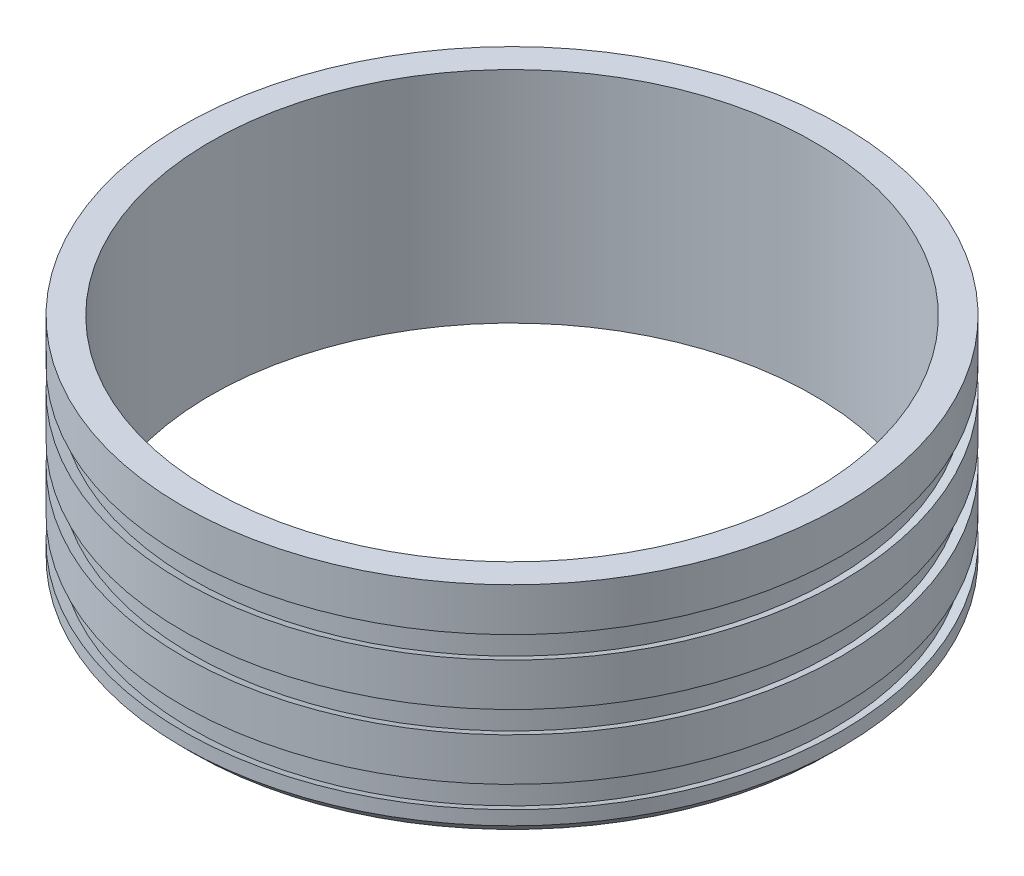
SolidWorks part; units mm, degrees
ref_plane "Front Plane" through (0, 0, 0) normal (0, 0, 1) x (1, 0, 0)
ref_plane "Top Plane" through (0, 0, 0) normal (0, 1, 0) x (1, 0, 0)
ref_plane "Right Plane" through (0, 0, 0) normal (1, 0, 0) x (0, 0, -1)
sketch "Sketch1" plane through (0, 0, 0) normal (0, 1, 0) x (1, 0, 0)
  circle A0 centre (0, 0) radius 76.25
  circle A1 centre (0, 0) radius 69.75
  dimension "D2" = 152.5
  dimension "D1" = 6.5
extrude "Boss-Extrude1" add sketch "Sketch1" along normal blind 50.8
sketch "Sketch2" plane through (0, 0, 0) normal (0, 0, 1) x (1, 0, 0)
  line L0 (-76.25, 40.8) -> (-76.25, 35.72) construction
  line L1 (-76.25, 40.8) -> (-76.25, 35.72)
  line L2 (-76.25, 50.8) -> (-76.25, 0) construction
  line L19 (0, 0) -> (0, 50.8) construction
  line L20 (-76.25, 0) -> (76.25, 0) construction
  line L21 (69.75, 50.8) -> (-69.75, 50.8) construction
  line L22 (-76.25, 40.8) -> (-74, 41.6189)
  line L23 (-74, 41.6189) -> (-74, 34.9011)
  line L24 (-74, 38.26) -> (-76.25, 38.26) construction
  line L25 (-76.25, 35.72) -> (-74, 34.9011)
  line L26 (-74, 26.6189) -> (-74, 19.9011)
  line L27 (-76.25, 20.72) -> (-74, 19.9011)
  line L28 (-76.25, 25.8) -> (-76.25, 20.72)
  line L29 (-76.25, 25.8) -> (-74, 26.6189)
  line L30 (-74, 11.6189) -> (-74, 4.9011)
  line L31 (-76.25, 5.72) -> (-74, 4.9011)
  line L32 (-76.25, 10.8) -> (-76.25, 5.72)
  line L33 (-76.25, 10.8) -> (-74, 11.6189)
  point P4 (-75.45, 25.7898)
  dimension "D2" = 2.25
  dimension "D3" = 110
  dimension "D1" = 5.08
  dimension "D4" = 3
revolve "Cut-Revolve1" cut sketch "Sketch2" angle 360 about L19
chamfer "Chamfer1" distance 2.5 angle 45 1 edges at (0, 0, 76.25)
